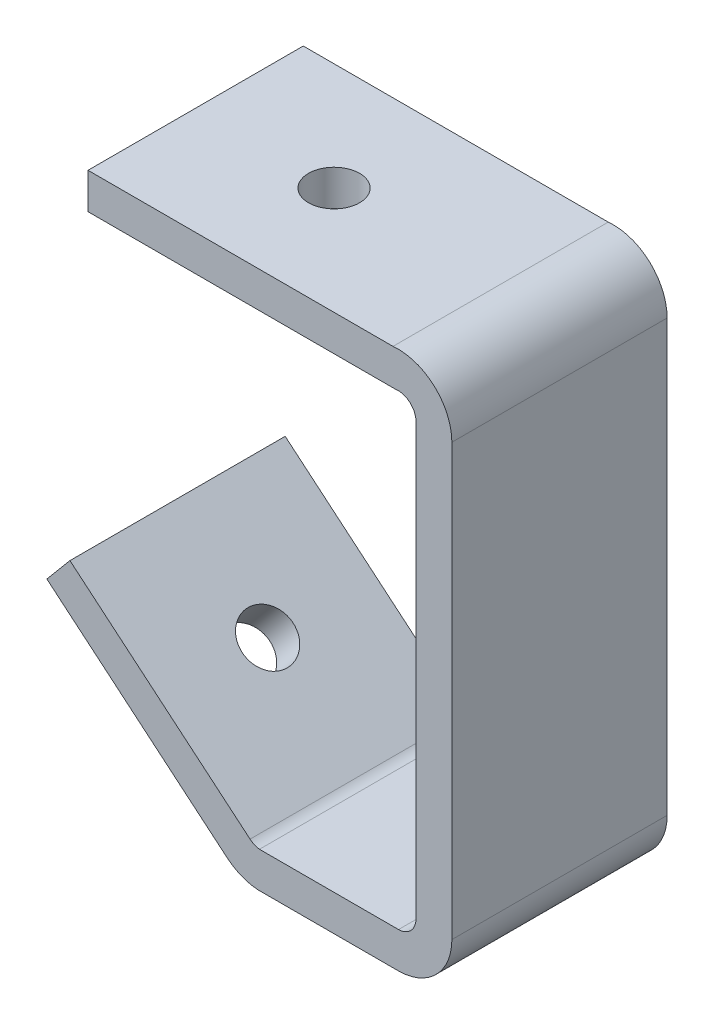
SolidWorks part; units mm, degrees
ref_plane "Front Plane" through (0, 0, 0) normal (0, 0, 1) x (1, 0, 0)
ref_plane "Top Plane" through (0, 0, 0) normal (0, 1, 0) x (1, 0, 0)
ref_plane "Right Plane" through (0, 0, 0) normal (1, 0, 0) x (0, 0, -1)
sketch "Sketch1" plane through (0, 0, 0) normal (0, 0, 1) x (1, 0, 0)
  line L0 (0, 0) -> (53.98, 0)
  line L1 (64.4014, -9.4882) -> (64.4014, -85.7212)
  line L2 (55.0251, -95.25) -> (30.0713, -95.25)
  line L3 (24.6021, -93.043) -> (-7.2807, -66.2902)
  line L4 (0, -6.35) -> (54.3576, -6.35)
  line L5 (58.0514, -9.4882) -> (58.0514, -85.7212)
  line L6 (54.9602, -88.9) -> (30.3491, -88.9)
  line L7 (28.6838, -88.1787) -> (-3.199, -61.4258)
  line L8 (0, 0) -> (0, -6.35)
  line L9 (-3.199, -61.4258) -> (-7.2807, -66.2902)
  arc A0 (53.98, 0) -> (64.4014, -9.4882) centre (54.8714, -9.4882) cw
  arc A1 (64.4014, -85.7212) -> (55.0251, -95.25) centre (54.8714, -85.7212) cw
  arc A2 (30.0713, -95.25) -> (24.6021, -93.043) centre (30.7279, -85.7426) cw
  arc A3 (54.3576, -6.35) -> (58.0514, -9.4882) centre (54.8714, -9.4882) cw
  arc A4 (58.0514, -85.7212) -> (54.9602, -88.9) centre (54.8714, -85.7212) cw
  arc A5 (30.3491, -88.9) -> (28.6838, -88.1787) centre (30.7279, -85.7426) cw
  dimension "D2" = 9.53
  dimension "D3" = 9.53
  dimension "D4" = 9.53
  dimension "D1" = 53.98
  dimension "D5" = 95.25
  dimension "D6" = 24.9538
  dimension "D7" = 41.62
  dimension "D8" = 140
  dimension "D9" = 6.35
extrude "Boss-Extrude1" add sketch "Sketch1" along normal blind 38.1
sketch "Sketch2" plane through (0, 0, 0) normal (0, 1, 0) x (1, 0, 0)
  line L0 (0, -19.05) -> (24.5, -19.05)
  line L1 (0, -38.1) -> (0, 0) construction
  circle A0 centre (24.5, -19.05) radius 4.52
  dimension "D2" = 9.04
  dimension "D1" = 24.5
extrude "Cut-Extrude1" cut sketch "Sketch2" against normal blind 38.1
sketch "Sketch3" plane through (-35.6498, -42.4857, 0) normal (-0.6428, -0.766, 0) x (0.766, -0.6428, 0)
  line L0 (78.6532, 38.1) -> (37.0332, 0)
  line L1 (37.0332, 0) -> (78.6532, 0) construction
  circle A0 centre (57.8432, 19.05) radius 4.515
  dimension "D1" = 9.03
extrude "Cut-Extrude2" cut sketch "Sketch3" against normal blind 10 contours A0
